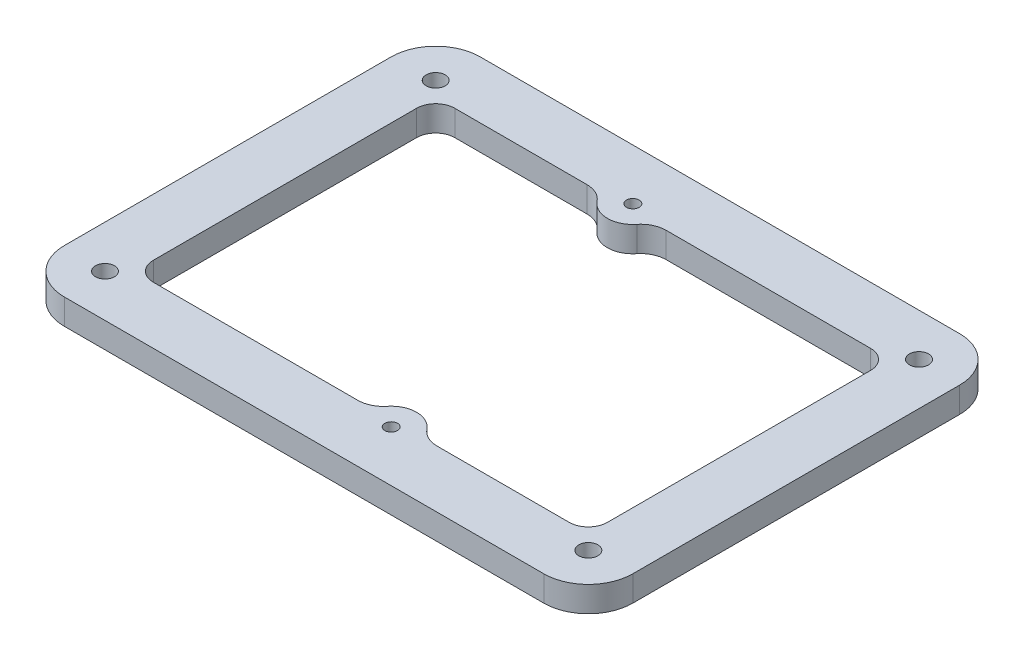
SolidWorks part; units mm, degrees
ref_plane "Front" through (0, 0, 0) normal (0, 0, 1) x (1, 0, 0)
ref_plane "Top" through (0, 0, 0) normal (0, 1, 0) x (1, 0, 0)
ref_plane "Right" through (0, 0, 0) normal (1, 0, 0) x (0, 0, -1)
sketch "草圖2" plane through (0, 0, 0) normal (0, 1, 0) x (-1, 0, 0)
  line L0 (-70.4577, 0) -> (70.2215, 0) construction
  line L1 (0, 52.2359) -> (0, -52.5789) construction
  line L2 (5.7, -24.7) -> (-5.7, 24.7) construction
  line L3 (32.6967, -32.6967) -> (-32.6967, -32.6967)
  line L4 (32.6967, -23.6967) -> (11.9424, -23.6967)
  line L5 (35.6967, -20.6967) -> (35.6967, 20.6967)
  line L6 (32.6967, 23.6967) -> (0.5424, 23.6967)
  line L7 (-35.6967, -20.6967) -> (-35.6967, 20.6967)
  line L8 (35.6967, -23.6967) -> (-35.6967, 23.6967) construction
  line L9 (35.6967, 23.6967) -> (-35.6967, -23.6967) construction
  line L10 (-44.6967, -20.6967) -> (-44.6967, 20.6967)
  line L11 (32.6967, 32.6967) -> (-32.6967, 32.6967)
  line L12 (44.6967, -20.6967) -> (44.6967, 20.6967)
  line L13 (44.6967, 20.6967) -> (35.6967, 20.6967) construction
  line L14 (32.6967, 32.6967) -> (32.6967, 23.6967) construction
  line L15 (5.7, -36.2246) -> (5.7, -13.1754) construction
  line L16 (-5.7, 34.3093) -> (-5.7, 15.0907) construction
  line L17 (32.6967, -23.6967) -> (-32.6967, -23.6967) construction
  line L18 (-0.5424, -23.6967) -> (-32.6967, -23.6967)
  line L19 (-32.6967, -32.6967) -> (-44.6967, -32.6967)
  line L20 (32.6967, 23.6967) -> (-32.6967, 23.6967) construction
  line L21 (-11.9424, 23.6967) -> (-32.6967, 23.6967)
  line L22 (-44.6967, 20.6967) -> (-44.6967, 32.6967)
  line L23 (-44.6967, -20.6967) -> (-44.6967, -32.6967)
  line L24 (-32.6967, 32.6967) -> (-44.6967, 32.6967)
  line L25 (32.6967, 32.6967) -> (44.6967, 32.6967)
  line L26 (44.6967, 20.6967) -> (44.6967, 32.6967)
  line L27 (44.6967, -20.6967) -> (44.6967, -32.6967)
  line L28 (32.6967, -32.6967) -> (44.6967, -32.6967)
  arc A0 (-35.6967, -20.6967) -> (-32.6967, -23.6967) centre (-32.6967, -20.6967) ccw
  arc A1 (35.6967, 20.6967) -> (32.6967, 23.6967) centre (32.6967, 20.6967) ccw
  arc A2 (32.6967, -23.6967) -> (35.6967, -20.6967) centre (32.6967, -20.6967) ccw
  circle A3 centre (38, 26) radius 1.5
  circle A4 centre (38, -26) radius 1.5
  circle A5 centre (-38, 26) radius 1.5
  circle A6 centre (-38, -26) radius 1.5
  circle A7 centre (5.7, -24.7) radius 1
  circle A8 centre (-5.7, 24.7) radius 1
  arc A9 (-32.6967, 23.6967) -> (-35.6967, 20.6967) centre (-32.6967, 20.6967) ccw
  arc A10 (-44.6967, -20.6967) -> (-32.6967, -32.6967) centre (-32.6967, -20.6967) ccw construction
  arc A11 (-32.6967, 32.6967) -> (-44.6967, 20.6967) centre (-32.6967, 20.6967) ccw construction
  arc A12 (44.6967, 20.6967) -> (32.6967, 32.6967) centre (32.6967, 20.6967) ccw construction
  arc A13 (32.6967, -32.6967) -> (44.6967, -20.6967) centre (32.6967, -20.6967) ccw construction
  arc A14 (35.6967, 20.6967) -> (32.6967, 23.6967) centre (32.6967, 20.6967) ccw construction
  arc A15 (40.1967, 20.6967) -> (32.6967, 28.1967) centre (32.6967, 20.6967) ccw construction
  arc A16 (8.8212, -22.1983) -> (2.5788, -22.1983) centre (5.7, -24.7) ccw
  arc A17 (8.8212, -22.1983) -> (11.9424, -23.6967) centre (11.9424, -19.6967) ccw
  arc A18 (2.5788, -22.1983) -> (-0.5424, -23.6967) centre (-0.5424, -19.6967) cw
  arc A19 (-2.5788, 22.1983) -> (-8.8212, 22.1983) centre (-5.7, 24.7) cw
  arc A20 (-2.5788, 22.1983) -> (0.5424, 23.6967) centre (0.5424, 19.6967) cw
  arc A21 (-8.8212, 22.1983) -> (-11.9424, 23.6967) centre (-11.9424, 19.6967) ccw
  point P4 (0, 0)
  point P7 (0, 0)
  point P23 (0, 0)
  point P25 (0, 0)
  point P31 (38, 26)
  point P56 (40.1967, 20.6967)
  point P58 (32.6967, 28.1967)
  point P60 (5.7, -24.7)
  point P68 (-5.7, 24.7)
  dimension "D6" = 3
  dimension "D7" = 2
  dimension "D8" = 3
  dimension "D10" = 4
  dimension "D11" = 4
  dimension "D1" = 52
  dimension "D2" = 76
  dimension "D4" = 11.4
  dimension "D5" = 49.4
  dimension "D9" = 9
  dimension "D3" = 2
extrude "填料-伸長1" add sketch "草圖2" along normal blind 4
fillet "圓角1" radius 7 4 edges at (44.6967, 2, -32.6967) (-44.6967, 2, -32.6967) (44.6967, 2, 32.6967) (-44.6967, 2, 32.6967)
